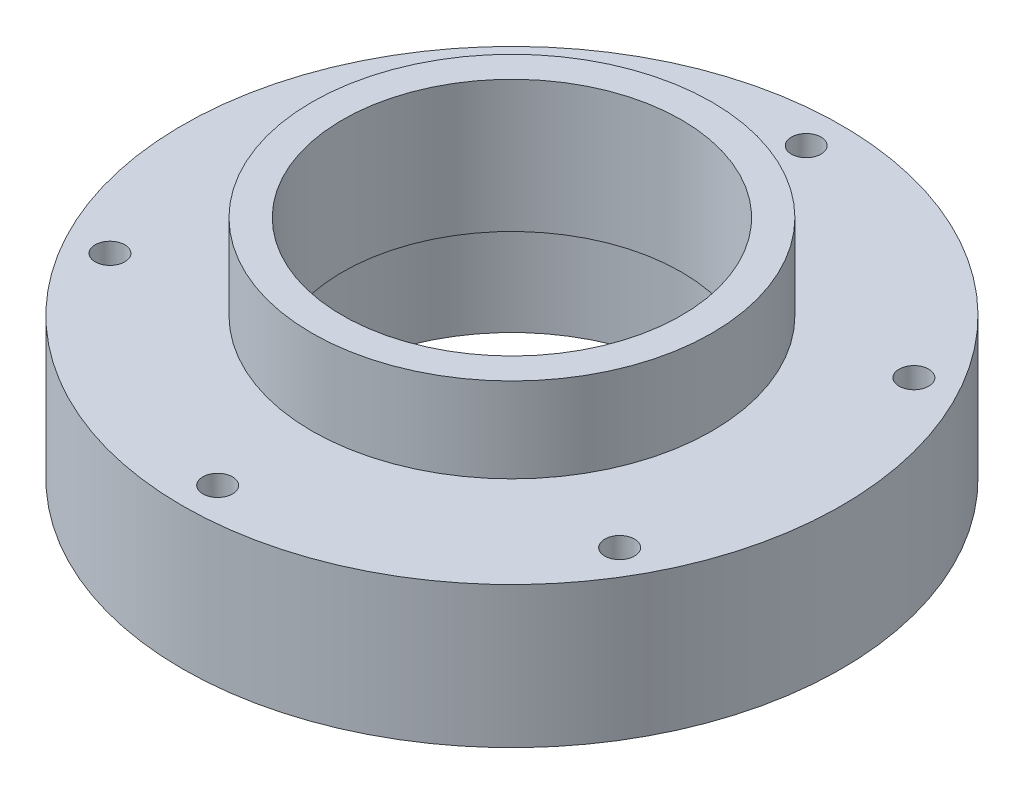
SolidWorks part; units mm, degrees
material "AISI 304"
ref_plane "Front" through (0, 0, 0) normal (0, 0, 1) x (1, 0, 0)
ref_plane "Top" through (0, 0, 0) normal (0, 1, 0) x (1, 0, 0)
ref_plane "Right" through (0, 0, 0) normal (1, 0, 0) x (0, 0, -1)
sketch "Sketch1" plane through (0, 0, 0) normal (0, 1, 0) x (1, 0, 0)
  circle A0 centre (0, 0) radius 17.78
  dimension "D1" = 35.56
extrude "Boss-Extrude1" add sketch "Sketch1" along normal blind 7.62
sketch "Sketch2" plane through (0, 7.62, 0) normal (0, 1, 0) x (1, 0, 0)
  circle A0 centre (0, 0) radius 10.795
  dimension "D1" = 21.59
extrude "Boss-Extrude2" add sketch "Sketch2" along normal blind 4.572
cosmetic thread "Cosmetic Thread4" parameters "D2"=20.32
hole_wizard "M2x0.4 Tapped Hole1" positions "Sketch9" profile "Sketch10" tap size "M2x0.4" standard "ANSI Metric" end condition through all
sketch "Sketch9" plane through (0, 0, 0) normal (0, -1, 0) x (-1, 0, 0)
  line L0 (0, 0) -> (0, 15.875)
  point P18 (0, 15.875)
  point P67 (13.7482, 7.9375)
  point P68 (13.7482, -7.9375)
  point P69 (0, -15.875)
  point P70 (-13.7482, -7.9375)
  point P71 (-13.7482, 7.9375)
  dimension "D1" = 15.875
  dimension "D2" = 6
sketch "Sketch10" plane through (0, 0, -15.875) normal (1, 0, 0) x (0, 0, -1)
  line L0 (0, 0) -> (0, 12.192)
  line L1 (0, 12.192) -> (0.8, 12.192)
  line L2 (0.8, 12.192) -> (0.8, 0)
  line L5 (0.8, 0) -> (0, 0)
  line L11 (0, -6.35) -> (0, 107.95) construction
  dimension "Thread Major Dia." = 1.6
  dimension "Thru Tap Drill Depth" = 12.192
hole_wizard "CBORE for M5 Hex Head Bolt1" positions "Sketch12" profile "Sketch13" counterbore size "M5" standard "BSI" end condition through all
sketch "Sketch12" plane through (0, 0, 0) normal (0, -1, 0) x (-1, 0, 0)
  point P0 (0, 0)
sketch "Sketch13" plane through (0, 0, 0) normal (1, 0, 0) x (0, 0, -1)
  line L0 (0, 0) -> (0, 12.192)
  line L1 (0, 12.192) -> (9.144, 12.192)
  line L3 (9.144, 12.192) -> (9.144, 5.08)
  line L4 (9.144, 5.08) -> (9.652, 5.08)
  line L5 (9.652, 5.08) -> (9.652, 0)
  line L7 (9.652, 0) -> (0, 0)
  line L11 (0, -6.35) -> (0, 107.95) construction
  dimension "Thru Hole Dia." = 18.288
  dimension "Thru Hole Depth" = 12.192
  dimension "C'Bore Dia." = 19.304
  dimension "C'Bore Depth" = 5.08
cosmetic thread "Cosmetic Thread6"
